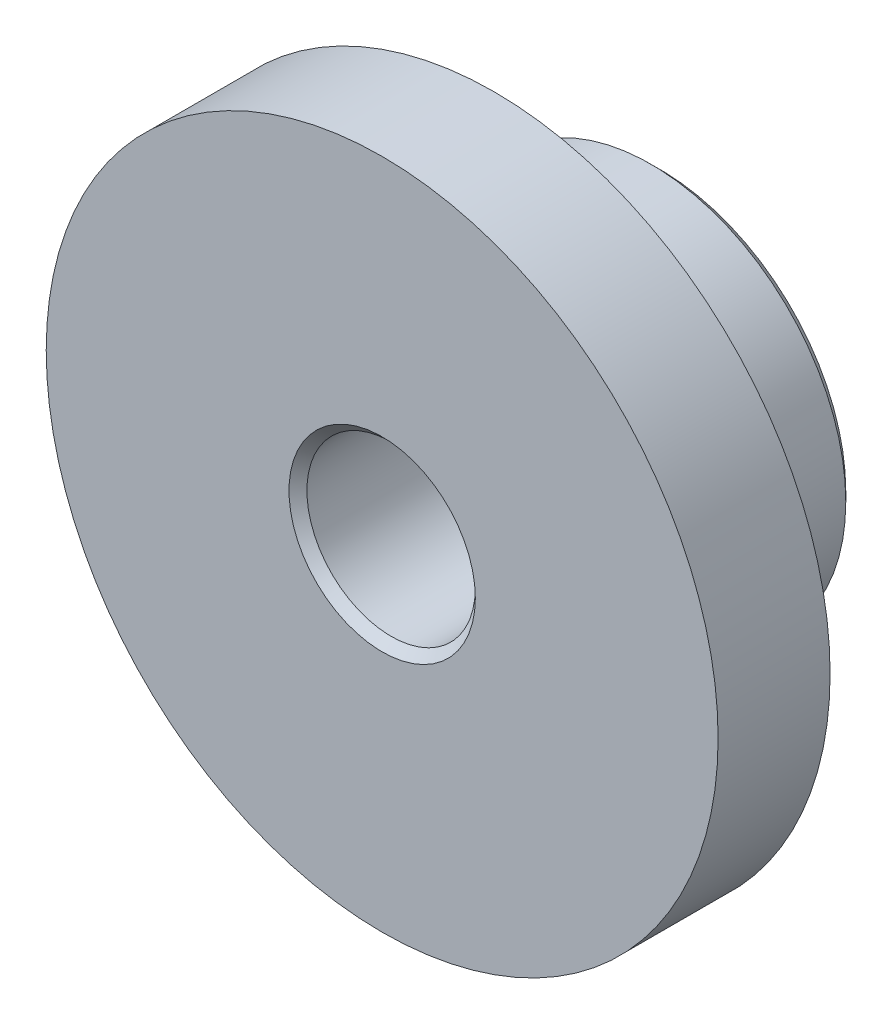
SolidWorks part; units mm, degrees
material "304 SSTL"
ref_plane "Front Plane" through (0, 0, 0) normal (0, 0, 1) x (1, 0, 0)
ref_plane "Top Plane" through (0, 0, 0) normal (0, 1, 0) x (1, 0, 0)
ref_plane "Right Plane" through (0, 0, 0) normal (1, 0, 0) x (0, 0, -1)
sketch "Sketch1" plane through (0, 0, 0) normal (0, 0, 1) x (1, 0, 0)
  circle A0 centre (0, 0) radius 19.05
  dimension "D1" = 38.1
extrude "Extrude1" add sketch "Sketch1" along normal blind 15.748
sketch "Sketch2" plane through (0, 0, 0) normal (0, 0, -1) x (-1, 0, 0)
  circle A0 centre (0, 0) radius 11.049
  circle A1 centre (0, 0) radius 19.05
  circle A2 centre (0, 0) radius 19.05 construction
  dimension "D1" = 22.098
extrude "Cut-Extrude1" cut sketch "Sketch2" against normal blind 9.398
sketch "Sketch3" plane through (0, 0, 15.748) normal (0, 0, 1) x (1, 0, 0)
  circle A0 centre (0, 0) radius 4.7752
  dimension "D1" = 9.5504
extrude "Cut-Extrude2" cut sketch "Sketch3" against normal blind 12.192
chamfer "Chamfer1" distance 0.508 angle 45 2 edges at (4.7752, 0, 15.748) (-11.049, 0, 0)
